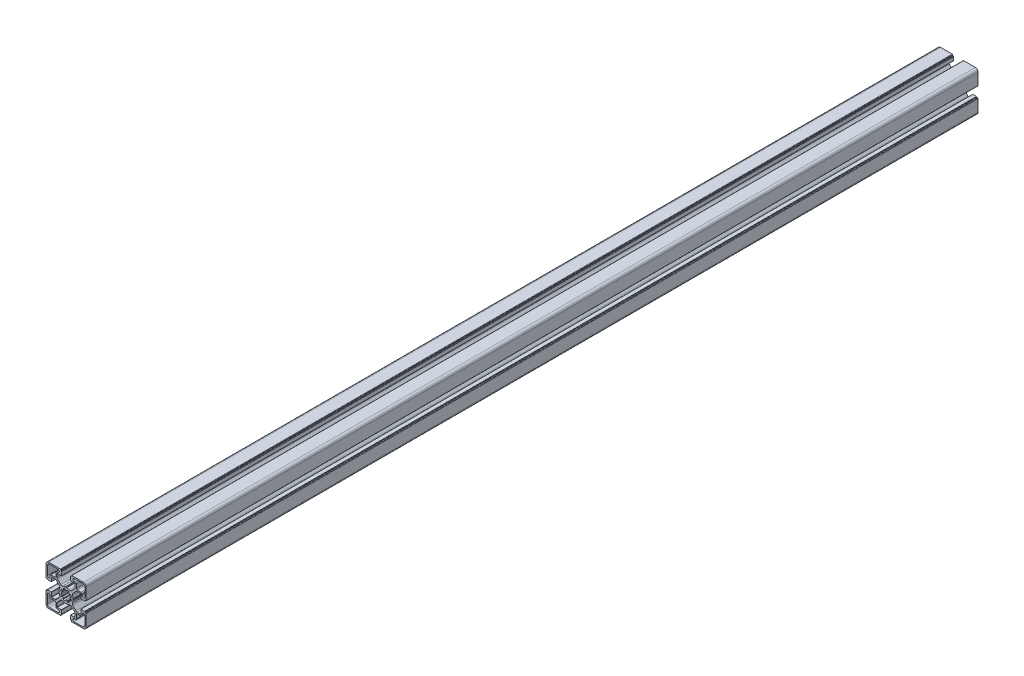
SolidWorks part; units mm, degrees
ref_plane "Front Plane" through (0, 0, 0) normal (0, 0, 1) x (1, 0, 0)
ref_plane "Top Plane" through (0, 0, 0) normal (0, 1, 0) x (1, 0, 0)
ref_plane "Right Plane" through (0, 0, 0) normal (1, 0, 0) x (0, 0, -1)
sketch "Sketch1" plane through (0, 0, 0) normal (0, 0, 1) x (1, 0, 0)
  line L0 (10.55, 18) -> (9, 18)
  line L1 (18.5, 21) -> (9, 21)
  line L2 (21, 9.0002) -> (21, 18.5)
  line L3 (18, 9.0002) -> (18, 10.55)
  line L4 (17, 11.55) -> (12.55, 11.55)
  line L5 (11.55, 12.55) -> (11.55, 17)
  line L6 (7.974, 0.7926) -> (7.5401, 0.0468)
  line L7 (-0.8674, 4.9242) -> (-0.9675, 5.4811)
  line L8 (-3.1913, 4.5626) -> (-2.864, 4.0985)
  line L9 (-4.0897, 2.8765) -> (-4.5668, 3.2082)
  line L10 (-5.4897, 0.9862) -> (-4.9205, 0.8878)
  line L11 (11.1298, 9.425) -> (7.5635, 5.8587)
  line L12 (16.3169, 9.9945) -> (12.5048, 9.9945)
  line L13 (16.5169, 5.2) -> (16.5169, 9.7945)
  line L14 (20.7196, 5) -> (16.7169, 5)
  line L15 (21.0196, 5.3) -> (21.0196, 5.5)
  line L16 (22, 5.8) -> (21.3196, 5.8)
  line L17 (22.5, 6.3) -> (22.5, 19.5)
  line L18 (19.5, 22.5) -> (6.3757, 22.5)
  line L19 (5.8757, 21.3) -> (5.8757, 22)
  line L20 (5.5757, 21) -> (5.3, 21)
  line L21 (5, 16.6668) -> (5, 20.7)
  line L22 (9.9054, 16.4668) -> (5.2, 16.4668)
  line L23 (10.1054, 12.4716) -> (10.1054, 16.2668)
  line L24 (5.9449, 7.4827) -> (9.5196, 11.0574)
  line L25 (0.1126, 7.6069) -> (0.7547, 7.9748)
  line L26 (5.4897, 0.9862) -> (4.9205, 0.8878)
  line L27 (4.0897, 2.8765) -> (4.5668, 3.2082)
  line L28 (3.1913, 4.5626) -> (2.864, 4.0985)
  line L29 (0.8674, 4.9242) -> (0.9675, 5.4811)
  line L30 (-10.55, -18) -> (-9, -18)
  line L31 (-18.5, -21) -> (-9, -21)
  line L32 (-21, -9.0002) -> (-21, -18.5)
  line L33 (-18, -9.0002) -> (-18, -10.55)
  line L34 (-17, -11.55) -> (-12.55, -11.55)
  line L35 (-11.55, -12.55) -> (-11.55, -17)
  line L36 (-7.974, -0.7926) -> (-7.5401, -0.0468)
  line L37 (-11.1298, -9.425) -> (-7.5635, -5.8587)
  line L38 (-16.3169, -9.9945) -> (-12.5048, -9.9945)
  line L39 (-16.5169, -5.2) -> (-16.5169, -9.7945)
  line L40 (-20.7196, -5) -> (-16.7169, -5)
  line L41 (-21.0196, -5.3) -> (-21.0196, -5.5)
  line L42 (-22, -5.8) -> (-21.3196, -5.8)
  line L43 (-22.5, -6.3) -> (-22.5, -19.5)
  line L44 (-19.5, -22.5) -> (-6.3757, -22.5)
  line L45 (-5.8757, -21.3) -> (-5.8757, -22)
  line L46 (-5.5757, -21) -> (-5.3, -21)
  line L47 (-5, -16.6668) -> (-5, -20.7)
  line L48 (-9.9054, -16.4668) -> (-5.2, -16.4668)
  line L49 (-10.1054, -12.4716) -> (-10.1054, -16.2668)
  line L50 (-5.9449, -7.4827) -> (-9.5196, -11.0574)
  line L51 (-0.1126, -7.6069) -> (-0.7547, -7.9748)
  line L52 (0.8674, -4.9242) -> (0.9675, -5.4811)
  line L53 (3.1913, -4.5626) -> (2.864, -4.0985)
  line L54 (4.0897, -2.8765) -> (4.5668, -3.2082)
  line L55 (5.4897, -0.9862) -> (4.9205, -0.8878)
  line L56 (0.1126, -7.6069) -> (0.7547, -7.9748)
  line L57 (5.9449, -7.4827) -> (9.5196, -11.0574)
  line L58 (10.1054, -12.4716) -> (10.1054, -16.2668)
  line L59 (9.9054, -16.4668) -> (5.2, -16.4668)
  line L60 (5, -16.6668) -> (5, -20.7)
  line L61 (5.5757, -21) -> (5.3, -21)
  line L62 (-0.1126, 7.6069) -> (-0.7547, 7.9748)
  line L63 (-5.9449, 7.4827) -> (-9.5196, 11.0574)
  line L64 (-10.1054, 12.4716) -> (-10.1054, 16.2668)
  line L65 (-9.9054, 16.4668) -> (-5.2, 16.4668)
  line L66 (-5, 16.6668) -> (-5, 20.7)
  line L67 (-5.5757, 21) -> (-5.3, 21)
  line L68 (-5.8757, 21.3) -> (-5.8757, 22)
  line L69 (-19.5, 22.5) -> (-6.3757, 22.5)
  line L70 (-22.5, 6.3) -> (-22.5, 19.5)
  line L71 (-22, 5.8) -> (-21.3196, 5.8)
  line L72 (-21.0196, 5.3) -> (-21.0196, 5.5)
  line L73 (-20.7196, 5) -> (-16.7169, 5)
  line L74 (-16.5169, 5.2) -> (-16.5169, 9.7945)
  line L75 (-16.3169, 9.9945) -> (-12.5048, 9.9945)
  line L76 (-11.1298, 9.425) -> (-7.5635, 5.8587)
  line L77 (-7.974, 0.7926) -> (-7.5401, 0.0468)
  line L78 (5.8757, -21.3) -> (5.8757, -22)
  line L79 (19.5, -22.5) -> (6.3757, -22.5)
  line L80 (22.5, -6.3) -> (22.5, -19.5)
  line L81 (22, -5.8) -> (21.3196, -5.8)
  line L82 (21.0196, -5.3) -> (21.0196, -5.5)
  line L83 (20.7196, -5) -> (16.7169, -5)
  line L84 (16.5169, -5.2) -> (16.5169, -9.7945)
  line L85 (16.3169, -9.9945) -> (12.5048, -9.9945)
  line L86 (11.1298, -9.425) -> (7.5635, -5.8587)
  line L87 (-5.4897, -0.9862) -> (-4.9205, -0.8878)
  line L88 (-4.0897, -2.8765) -> (-4.5668, -3.2082)
  line L89 (-3.1913, -4.5626) -> (-2.864, -4.0985)
  line L90 (-0.8674, -4.9242) -> (-0.9675, -5.4811)
  line L91 (7.974, -0.7926) -> (7.5401, -0.0468)
  line L92 (-11.55, 12.55) -> (-11.55, 17)
  line L93 (-17, 11.55) -> (-12.55, 11.55)
  line L94 (-18, 9.0002) -> (-18, 10.55)
  line L95 (-21, 9.0002) -> (-21, 18.5)
  line L96 (-18.5, 21) -> (-9, 21)
  line L97 (-10.55, 18) -> (-9, 18)
  line L98 (11.55, -12.55) -> (11.55, -17)
  line L99 (17, -11.55) -> (12.55, -11.55)
  line L100 (18, -9.0002) -> (18, -10.55)
  line L101 (21, -9.0002) -> (21, -18.5)
  line L102 (18.5, -21) -> (9, -21)
  line L103 (10.55, -18) -> (9, -18)
  line L104 (-33.3633, 0) -> (37.7265, 0) construction
  line L105 (0, 32.2957) -> (0, -36.0465) construction
  arc A0 (9, 18) -> (9, 21) centre (9, 19.5) cw
  arc A1 (18.5, 21) -> (21, 18.5) centre (18.5, 18.5) cw
  arc A2 (21, 9.0002) -> (18, 9.0002) centre (19.5, 9.0002) cw
  arc A3 (17, 11.55) -> (18, 10.55) centre (17, 10.55) cw
  arc A4 (12.55, 11.55) -> (11.55, 12.55) centre (12.55, 12.55) cw
  arc A5 (10.55, 18) -> (11.55, 17) centre (10.55, 17) cw
  arc A6 (7.5313, 0) -> (7.5401, 0.0468) centre (7.7309, -0.013) cw
  arc A7 (8, 0.9141) -> (7.974, 0.7926) centre (7.8011, 0.8932) cw
  arc A8 (7.2004, 3.6119) -> (8, 0.9141) centre (0.0496, 0.0249) cw
  arc A9 (7.2004, 3.6119) -> (7.5635, 5.8587) centre (8.9385, 4.4837) cw
  arc A10 (11.1298, 9.425) -> (12.5048, 9.9945) centre (12.5048, 8.05) cw
  arc A11 (16.3169, 9.9945) -> (16.5169, 9.7945) centre (16.3169, 9.7945) cw
  arc A12 (16.7169, 5) -> (16.5169, 5.2) centre (16.7169, 5.2) cw
  arc A13 (21.0196, 5.3) -> (20.7196, 5) centre (20.7196, 5.3) cw
  arc A14 (0.8674, 4.9242) -> (-0.8674, 4.9242) centre (0, 0) ccw
  arc A15 (-0.9675, 5.4811) -> (-1.5951, 5.8941) centre (-1.4627, 5.4119) ccw
  arc A16 (-1.5951, 5.8941) -> (-3.0444, 5.2994) centre (-0.0235, 0) ccw
  arc A17 (-3.0444, 5.2994) -> (-3.1913, 4.5626) centre (-2.7943, 4.8665) ccw
  arc A18 (-2.864, 4.0985) -> (-4.0897, 2.8765) centre (0, 0) ccw
  arc A19 (-4.5668, 3.2082) -> (-5.3025, 3.0565) centre (-4.868, 2.8091) ccw
  arc A20 (-5.3025, 3.0565) -> (-5.9068, 1.6112) centre (-0.0235, 0) ccw
  arc A21 (-5.9068, 1.6112) -> (-5.4897, 0.9862) centre (-5.4239, 1.4819) ccw
  arc A22 (-4.9205, 0.8878) -> (-5, 0) centre (0, 0) ccw
  arc A23 (21.0196, 5.5) -> (21.3196, 5.8) centre (21.3196, 5.5) cw
  arc A24 (22.5, 6.3) -> (22, 5.8) centre (22, 6.3) cw
  arc A25 (19.5, 22.5) -> (22.5, 19.5) centre (19.5, 19.5) cw
  arc A26 (5.8757, 22) -> (6.3757, 22.5) centre (6.3757, 22) cw
  arc A27 (5.8757, 21.3) -> (5.5757, 21) centre (5.5757, 21.3) cw
  arc A28 (5, 20.7) -> (5.3, 21) centre (5.3, 20.7) cw
  arc A29 (5.2, 16.4668) -> (5, 16.6668) centre (5.2, 16.6668) cw
  arc A30 (9.9054, 16.4668) -> (10.1054, 16.2668) centre (9.9054, 16.2668) cw
  arc A31 (10.1054, 12.4716) -> (9.5196, 11.0574) centre (8.1054, 12.4716) cw
  arc A32 (5.9449, 7.4827) -> (3.6665, 7.1733) centre (4.5855, 8.9496) cw
  arc A33 (0.8764, 8) -> (3.6665, 7.1733) centre (0.0235, 0) cw
  arc A34 (0.7547, 7.9748) -> (0.8764, 8) centre (0.8542, 7.8013) cw
  arc A35 (0.1126, 7.6069) -> (0, 7.531) centre (-0.0489, 7.7249) cw
  arc A36 (4.9205, 0.8878) -> (5, 0) centre (0, 0) cw
  arc A37 (5.9068, 1.6112) -> (5.4897, 0.9862) centre (5.4239, 1.4819) cw
  arc A38 (5.3025, 3.0565) -> (5.9068, 1.6112) centre (0.0235, 0) cw
  arc A39 (4.5668, 3.2082) -> (5.3025, 3.0565) centre (4.868, 2.8091) cw
  arc A40 (2.864, 4.0985) -> (4.0897, 2.8765) centre (0, 0) cw
  arc A41 (3.0444, 5.2994) -> (3.1913, 4.5626) centre (2.7943, 4.8665) cw
  arc A42 (1.5951, 5.8941) -> (3.0444, 5.2994) centre (0.0235, 0) cw
  arc A43 (0.9675, 5.4811) -> (1.5951, 5.8941) centre (1.4627, 5.4119) cw
  arc A44 (-9, -18) -> (-9, -21) centre (-9, -19.5) cw
  arc A45 (-18.5, -21) -> (-21, -18.5) centre (-18.5, -18.5) cw
  arc A46 (-21, -9.0002) -> (-18, -9.0002) centre (-19.5, -9.0002) cw
  arc A47 (-17, -11.55) -> (-18, -10.55) centre (-17, -10.55) cw
  arc A48 (-12.55, -11.55) -> (-11.55, -12.55) centre (-12.55, -12.55) cw
  arc A49 (-10.55, -18) -> (-11.55, -17) centre (-10.55, -17) cw
  arc A50 (-7.5313, 0) -> (-7.5401, -0.0468) centre (-7.7309, 0.013) cw
  arc A51 (-8, -0.9141) -> (-7.974, -0.7926) centre (-7.8011, -0.8932) cw
  arc A52 (-7.2004, -3.6119) -> (-8, -0.9141) centre (-0.0496, -0.0249) cw
  arc A53 (-7.2004, -3.6119) -> (-7.5635, -5.8587) centre (-8.9385, -4.4837) cw
  arc A54 (-11.1298, -9.425) -> (-12.5048, -9.9945) centre (-12.5048, -8.05) cw
  arc A55 (-16.3169, -9.9945) -> (-16.5169, -9.7945) centre (-16.3169, -9.7945) cw
  arc A56 (-16.7169, -5) -> (-16.5169, -5.2) centre (-16.7169, -5.2) cw
  arc A57 (-21.0196, -5.3) -> (-20.7196, -5) centre (-20.7196, -5.3) cw
  arc A58 (-21.0196, -5.5) -> (-21.3196, -5.8) centre (-21.3196, -5.5) cw
  arc A59 (-22.5, -6.3) -> (-22, -5.8) centre (-22, -6.3) cw
  arc A60 (-19.5, -22.5) -> (-22.5, -19.5) centre (-19.5, -19.5) cw
  arc A61 (-5.8757, -22) -> (-6.3757, -22.5) centre (-6.3757, -22) cw
  arc A62 (-5.8757, -21.3) -> (-5.5757, -21) centre (-5.5757, -21.3) cw
  arc A63 (-5, -20.7) -> (-5.3, -21) centre (-5.3, -20.7) cw
  arc A64 (-5.2, -16.4668) -> (-5, -16.6668) centre (-5.2, -16.6668) cw
  arc A65 (-9.9054, -16.4668) -> (-10.1054, -16.2668) centre (-9.9054, -16.2668) cw
  arc A66 (-10.1054, -12.4716) -> (-9.5196, -11.0574) centre (-8.1054, -12.4716) cw
  arc A67 (-5.9449, -7.4827) -> (-3.6665, -7.1733) centre (-4.5855, -8.9496) cw
  arc A68 (-0.8764, -8) -> (-3.6665, -7.1733) centre (-0.0235, 0) cw
  arc A69 (-0.7547, -7.9748) -> (-0.8764, -8) centre (-0.8542, -7.8013) cw
  arc A70 (-0.1126, -7.6069) -> (0, -7.531) centre (0.0489, -7.7249) cw
  arc A71 (0.9675, -5.4811) -> (1.5951, -5.8941) centre (1.4627, -5.4119) ccw
  arc A72 (1.5951, -5.8941) -> (3.0444, -5.2994) centre (0.0235, 0) ccw
  arc A73 (3.0444, -5.2994) -> (3.1913, -4.5626) centre (2.7943, -4.8665) ccw
  arc A74 (2.864, -4.0985) -> (4.0897, -2.8765) centre (0, 0) ccw
  arc A75 (4.5668, -3.2082) -> (5.3025, -3.0565) centre (4.868, -2.8091) ccw
  arc A76 (5.3025, -3.0565) -> (5.9068, -1.6112) centre (0.0235, 0) ccw
  arc A77 (5.9068, -1.6112) -> (5.4897, -0.9862) centre (5.4239, -1.4819) ccw
  arc A78 (4.9205, -0.8878) -> (5, 0) centre (0, 0) ccw
  arc A79 (0.1126, -7.6069) -> (0, -7.531) centre (-0.0489, -7.7249) ccw
  arc A80 (0.7547, -7.9748) -> (0.8764, -8) centre (0.8542, -7.8013) ccw
  arc A81 (0.8764, -8) -> (3.6665, -7.1733) centre (0.0235, 0) ccw
  arc A82 (5.9449, -7.4827) -> (3.6665, -7.1733) centre (4.5855, -8.9496) ccw
  arc A83 (10.1054, -12.4716) -> (9.5196, -11.0574) centre (8.1054, -12.4716) ccw
  arc A84 (9.9054, -16.4668) -> (10.1054, -16.2668) centre (9.9054, -16.2668) ccw
  arc A85 (5.2, -16.4668) -> (5, -16.6668) centre (5.2, -16.6668) ccw
  arc A86 (5, -20.7) -> (5.3, -21) centre (5.3, -20.7) ccw
  arc A87 (5.8757, -21.3) -> (5.5757, -21) centre (5.5757, -21.3) ccw
  arc A88 (-0.1126, 7.6069) -> (0, 7.531) centre (0.0489, 7.7249) ccw
  arc A89 (-0.7547, 7.9748) -> (-0.8764, 8) centre (-0.8542, 7.8013) ccw
  arc A90 (-0.8764, 8) -> (-3.6665, 7.1733) centre (-0.0235, 0) ccw
  arc A91 (-5.9449, 7.4827) -> (-3.6665, 7.1733) centre (-4.5855, 8.9496) ccw
  arc A92 (-10.1054, 12.4716) -> (-9.5196, 11.0574) centre (-8.1054, 12.4716) ccw
  arc A93 (-9.9054, 16.4668) -> (-10.1054, 16.2668) centre (-9.9054, 16.2668) ccw
  arc A94 (-5.2, 16.4668) -> (-5, 16.6668) centre (-5.2, 16.6668) ccw
  arc A95 (-5, 20.7) -> (-5.3, 21) centre (-5.3, 20.7) ccw
  arc A96 (-5.8757, 21.3) -> (-5.5757, 21) centre (-5.5757, 21.3) ccw
  arc A97 (-5.8757, 22) -> (-6.3757, 22.5) centre (-6.3757, 22) ccw
  arc A98 (-19.5, 22.5) -> (-22.5, 19.5) centre (-19.5, 19.5) ccw
  arc A99 (-22.5, 6.3) -> (-22, 5.8) centre (-22, 6.3) ccw
  arc A100 (-21.0196, 5.5) -> (-21.3196, 5.8) centre (-21.3196, 5.5) ccw
  arc A101 (-21.0196, 5.3) -> (-20.7196, 5) centre (-20.7196, 5.3) ccw
  arc A102 (-16.7169, 5) -> (-16.5169, 5.2) centre (-16.7169, 5.2) ccw
  arc A103 (-16.3169, 9.9945) -> (-16.5169, 9.7945) centre (-16.3169, 9.7945) ccw
  arc A104 (-11.1298, 9.425) -> (-12.5048, 9.9945) centre (-12.5048, 8.05) ccw
  arc A105 (-7.2004, 3.6119) -> (-7.5635, 5.8587) centre (-8.9385, 4.4837) ccw
  arc A106 (-7.2004, 3.6119) -> (-8, 0.9141) centre (-0.0496, 0.0249) ccw
  arc A107 (-8, 0.9141) -> (-7.974, 0.7926) centre (-7.8011, 0.8932) ccw
  arc A108 (-7.5313, 0) -> (-7.5401, 0.0468) centre (-7.7309, -0.013) ccw
  arc A109 (5.8757, -22) -> (6.3757, -22.5) centre (6.3757, -22) ccw
  arc A110 (19.5, -22.5) -> (22.5, -19.5) centre (19.5, -19.5) ccw
  arc A111 (22.5, -6.3) -> (22, -5.8) centre (22, -6.3) ccw
  arc A112 (21.0196, -5.5) -> (21.3196, -5.8) centre (21.3196, -5.5) ccw
  arc A113 (-4.9205, -0.8878) -> (-5, 0) centre (0, 0) cw
  arc A114 (-5.9068, -1.6112) -> (-5.4897, -0.9862) centre (-5.4239, -1.4819) cw
  arc A115 (-5.3025, -3.0565) -> (-5.9068, -1.6112) centre (-0.0235, 0) cw
  arc A116 (-4.5668, -3.2082) -> (-5.3025, -3.0565) centre (-4.868, -2.8091) cw
  arc A117 (-2.864, -4.0985) -> (-4.0897, -2.8765) centre (0, 0) cw
  arc A118 (-3.0444, -5.2994) -> (-3.1913, -4.5626) centre (-2.7943, -4.8665) cw
  arc A119 (-1.5951, -5.8941) -> (-3.0444, -5.2994) centre (-0.0235, 0) cw
  arc A120 (-0.9675, -5.4811) -> (-1.5951, -5.8941) centre (-1.4627, -5.4119) cw
  arc A121 (0.8674, -4.9242) -> (-0.8674, -4.9242) centre (0, 0) cw
  arc A122 (21.0196, -5.3) -> (20.7196, -5) centre (20.7196, -5.3) ccw
  arc A123 (16.7169, -5) -> (16.5169, -5.2) centre (16.7169, -5.2) ccw
  arc A124 (-10.55, 18) -> (-11.55, 17) centre (-10.55, 17) ccw
  arc A125 (-12.55, 11.55) -> (-11.55, 12.55) centre (-12.55, 12.55) ccw
  arc A126 (-17, 11.55) -> (-18, 10.55) centre (-17, 10.55) ccw
  arc A127 (-21, 9.0002) -> (-18, 9.0002) centre (-19.5, 9.0002) ccw
  arc A128 (-18.5, 21) -> (-21, 18.5) centre (-18.5, 18.5) ccw
  arc A129 (-9, 18) -> (-9, 21) centre (-9, 19.5) ccw
  arc A130 (16.3169, -9.9945) -> (16.5169, -9.7945) centre (16.3169, -9.7945) ccw
  arc A131 (11.1298, -9.425) -> (12.5048, -9.9945) centre (12.5048, -8.05) ccw
  arc A132 (7.2004, -3.6119) -> (7.5635, -5.8587) centre (8.9385, -4.4837) ccw
  arc A133 (7.2004, -3.6119) -> (8, -0.9141) centre (0.0496, -0.0249) ccw
  arc A134 (8, -0.9141) -> (7.974, -0.7926) centre (7.8011, -0.8932) ccw
  arc A135 (7.5313, 0) -> (7.5401, -0.0468) centre (7.7309, 0.013) ccw
  arc A136 (10.55, -18) -> (11.55, -17) centre (10.55, -17) ccw
  arc A137 (12.55, -11.55) -> (11.55, -12.55) centre (12.55, -12.55) ccw
  arc A138 (17, -11.55) -> (18, -10.55) centre (17, -10.55) ccw
  arc A139 (21, -9.0002) -> (18, -9.0002) centre (19.5, -9.0002) ccw
  arc A140 (18.5, -21) -> (21, -18.5) centre (18.5, -18.5) ccw
  arc A141 (9, -18) -> (9, -21) centre (9, -19.5) ccw
  dimension "D6" = 12.2
  dimension "D8" = 10
  dimension "D1" = 10
  dimension "D2" = 45
  dimension "D3" = 45
  dimension "D4" = 10
  dimension "D5" = 14.5
  dimension "D7" = 22.5
extrude "Base-Extrude" add sketch "Sketch1" against normal blind 1000
